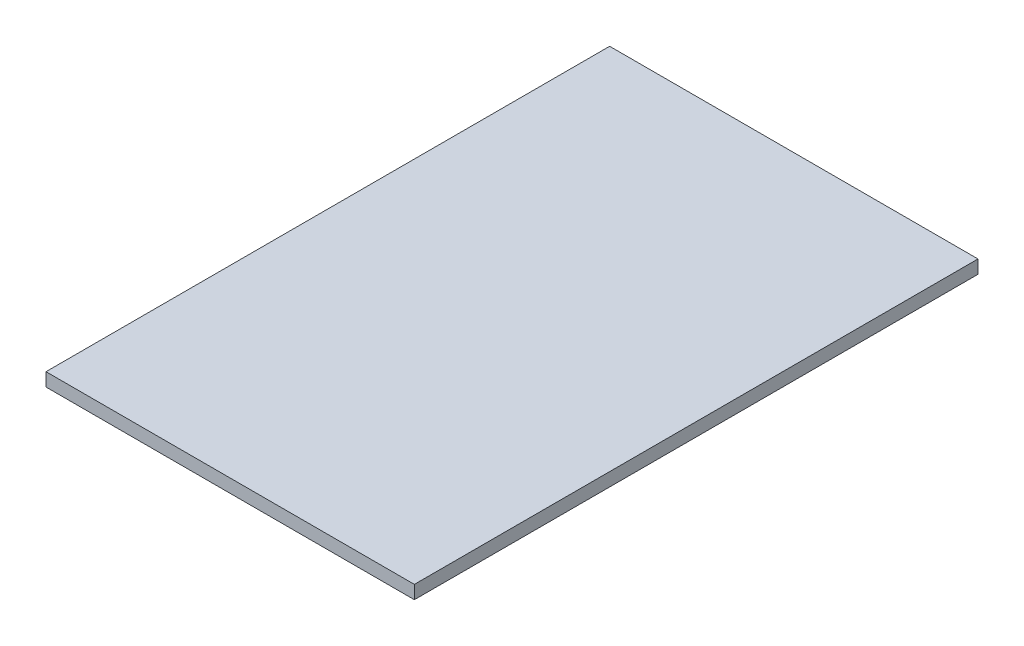
SolidWorks part; units mm, degrees
ref_plane "Спереди" through (0, 0, 0) normal (0, 0, 1) x (1, 0, 0)
ref_plane "Сверху" through (0, 0, 0) normal (0, 1, 0) x (1, 0, 0)
ref_plane "Справа" through (0, 0, 0) normal (1, 0, 0) x (0, 0, -1)
sketch "Эскиз1" plane through (0, 0, 0) normal (0, 1, 0) x (1, 0, 0)
  line L1 (249, -381) -> (-249, -381)
  line L2 (249, -381) -> (249, 381)
  line L3 (249, 381) -> (-249, 381)
  line L4 (-249, -381) -> (-249, 381)
  line L5 (249, -381) -> (-249, 381) construction
  line L6 (249, 381) -> (-249, -381) construction
  point P0 (0, 0)
  dimension "D1" = 762
  dimension "D2" = 498
extrude "Бобышка-Вытянуть1" add sketch "Эскиз1" along normal blind 18
